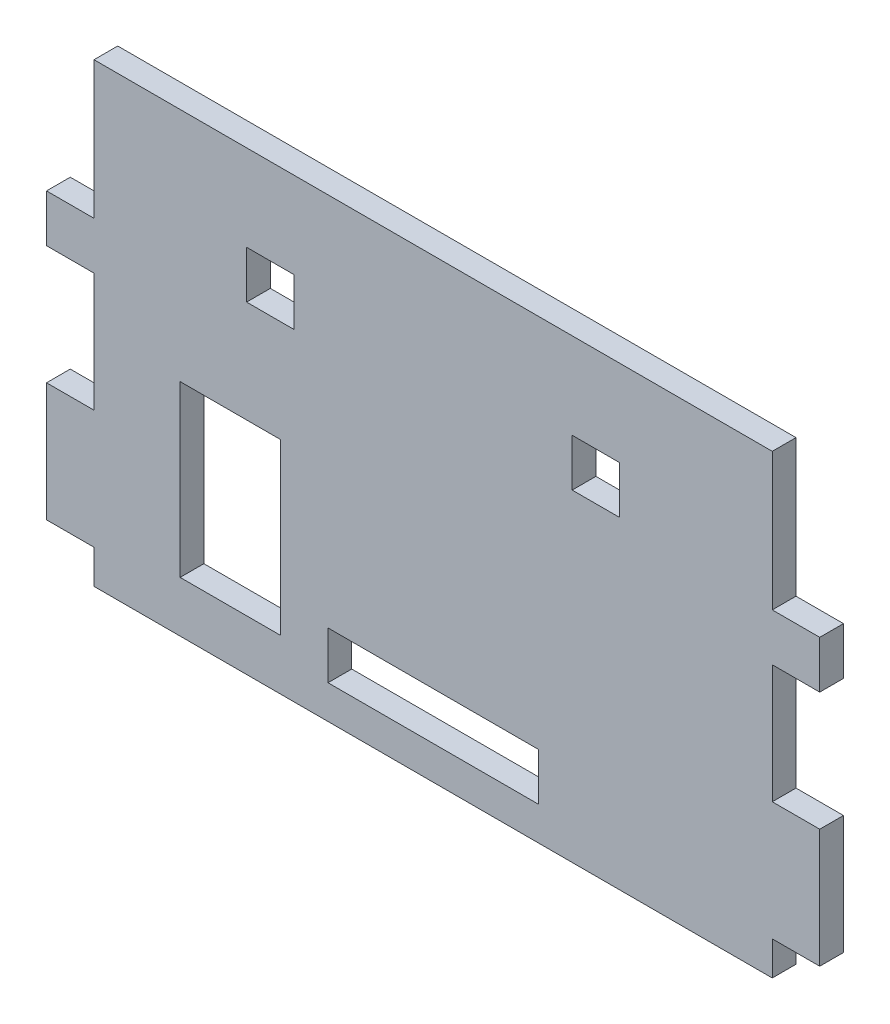
SolidWorks part; units mm, degrees
material "Maple"
ref_plane "Front Plane" through (0, 0, 0) normal (0, 0, 1) x (1, 0, 0)
ref_plane "Top Plane" through (0, 0, 0) normal (0, 1, 0) x (1, 0, 0)
ref_plane "Right Plane" through (0, 0, 0) normal (1, 0, 0) x (0, 0, -1)
sketch "Sketch1" plane through (0, 0, 0) normal (0, 0, 1) x (1, 0, 0)
  line L0 (-200, 45) -> (-200, 80)
  line L1 (-200, 0) -> (0, 0)
  line L2 (-200, 0) -> (-200, 10)
  line L3 (-200, 134.5) -> (0, 134.5)
  line L4 (0, 0) -> (0, 10)
  line L5 (-200, 94) -> (-200, 134.5)
  line L6 (-100, 0) -> (-100, 134.5) construction
  line L7 (0, 94) -> (14, 94)
  line L8 (-214, 80) -> (-200, 80)
  line L9 (-214, 80) -> (-214, 94)
  line L10 (-214, 94) -> (-200, 94)
  line L11 (14, 80) -> (14, 94)
  line L12 (-155, 109.1) -> (-141, 109.1)
  line L13 (-155, 109.1) -> (-155, 95.1)
  line L14 (-214, 10) -> (-200, 10)
  line L15 (-214, 10) -> (-214, 45)
  line L16 (-214, 45) -> (-200, 45)
  line L17 (14, 10) -> (14, 45)
  line L18 (-155, 95.1) -> (-141, 95.1)
  line L19 (-141, 109.1) -> (-141, 95.1)
  line L20 (-155, 109.1) -> (-141, 95.1) construction
  line L21 (-155, 95.1) -> (-141, 109.1) construction
  line L22 (-59, 95.1) -> (-45, 95.1)
  line L23 (-59, 95.1) -> (-59, 109.1)
  line L24 (-59, 109.1) -> (-45, 109.1)
  line L25 (-45, 95.1) -> (-45, 109.1)
  line L26 (0, 10) -> (14, 10)
  line L27 (-59, 95.1) -> (-45, 109.1) construction
  line L28 (0, 80) -> (14, 80)
  line L29 (-59, 109.1) -> (-45, 95.1) construction
  line L30 (0, 45) -> (14, 45)
  line L31 (-145, 15) -> (-174.6, 15)
  line L32 (-145, 15) -> (-145, 65)
  line L33 (0, 45) -> (0, 80)
  line L34 (0, 94) -> (0, 134.5)
  line L35 (-145, 65) -> (-174.6, 65)
  line L36 (-174.6, 15) -> (-174.6, 65)
  line L38 (-131, 23.9) -> (-69, 23.9)
  line L39 (-131, 23.9) -> (-131, 9.9)
  line L40 (-131, 9.9) -> (-69, 9.9)
  line L41 (-69, 23.9) -> (-69, 9.9)
  line L42 (-131, 23.9) -> (-69, 9.9) construction
  line L43 (-131, 9.9) -> (-69, 23.9) construction
  point P0 (0, 0)
  point P6 (-148, 102.1)
  point P21 (-52, 102.1)
  point P36 (-100, 16.9)
  dimension "D1" = 10
  dimension "D2" = 200
  dimension "D3" = 14
  dimension "D4" = 40.5
  dimension "D5" = 89.5
  dimension "D6" = 35
  dimension "D7" = 14
  dimension "D8" = 14
  dimension "D9" = 45
  dimension "D10" = 25.4
  dimension "D11" = 45
  dimension "D12" = 25.4
  dimension "D13" = 29.6
  dimension "D14" = 15
  dimension "D15" = 50
  dimension "D16" = 62
  dimension "D17" = 14
  dimension "D18" = 9.9
extrude "Boss-Extrude1" add sketch "Sketch1" along normal blind 7
